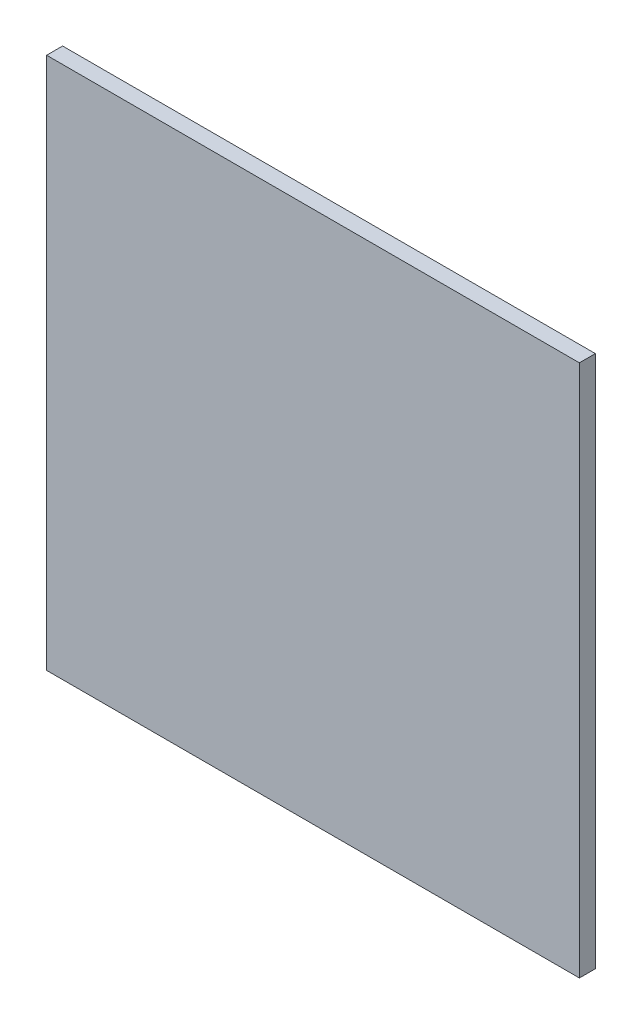
SolidWorks part; units mm, degrees
ref_plane "Front Plane" through (0, 0, 0) normal (0, 0, 1) x (1, 0, 0)
ref_plane "Top Plane" through (0, 0, 0) normal (0, 1, 0) x (1, 0, 0)
ref_plane "Right Plane" through (0, 0, 0) normal (1, 0, 0) x (0, 0, -1)
sketch "Sketch1" plane through (0, 0, 0) normal (0, 0, 1) x (1, 0, 0)
  line L0 (87.0968, 78.2258) -> (87.0968, -21.7742)
  line L1 (-112.9032, 78.2258) -> (87.0968, 78.2258)
  line L2 (-112.9032, 78.2258) -> (-112.9032, -121.7742)
  line L3 (-112.9032, -121.7742) -> (87.0968, -121.7742)
  line L4 (87.0968, -21.7742) -> (87.0968, -121.7742)
  dimension "D1" = 200
  dimension "D2" = 200
extrude "Boss-Extrude1" add sketch "Sketch1" along normal blind 6
